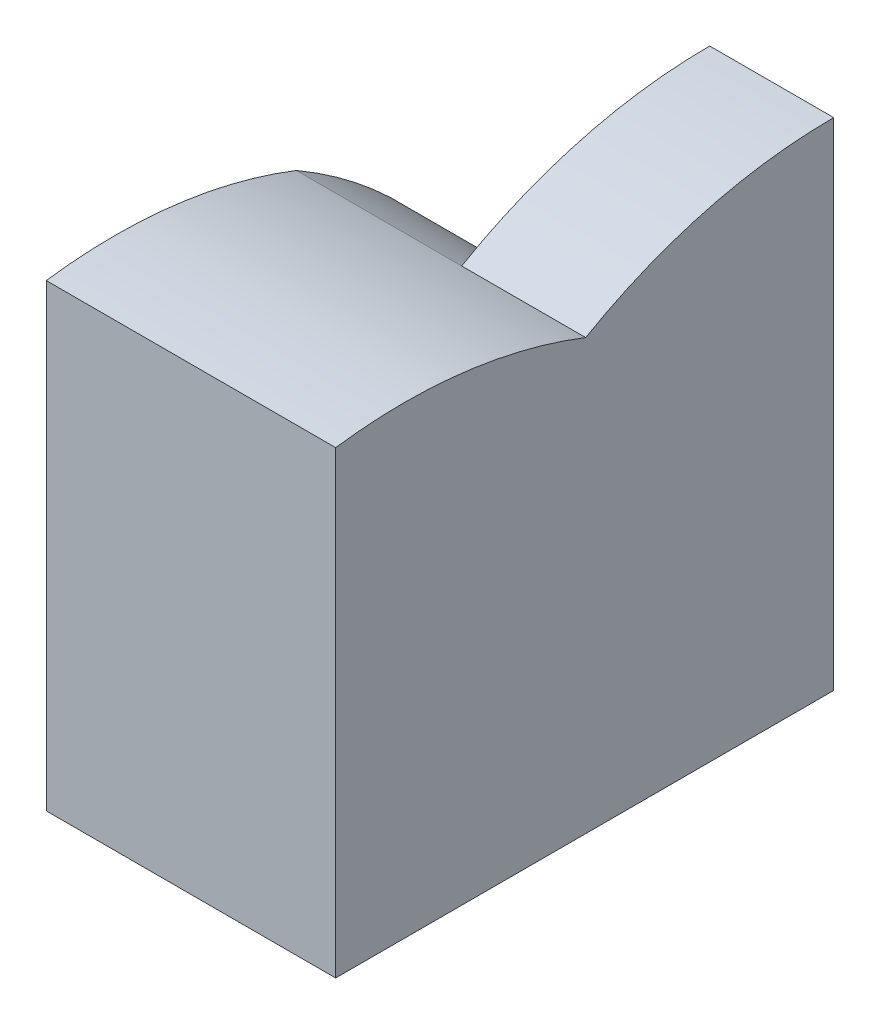
SolidWorks part; units mm, degrees
ref_plane "Front Plane" through (0, 0, 0) normal (0, 0, 1) x (1, 0, 0)
ref_plane "Top Plane" through (0, 0, 0) normal (0, 1, 0) x (1, 0, 0)
ref_plane "Right Plane" through (0, 0, 0) normal (1, 0, 0) x (0, 0, -1)
sketch "Sketch1" plane through (0, 0, 0) normal (1, 0, 0) x (0, 0, -1)
  line L0 (-6, 0) -> (0, 0)
  line L1 (0, 0) -> (0, 6)
  line L2 (-3, 0) -> (-3, 5.1962)
  arc A0 (-6, 0) -> (0, 6) centre (0, 0) cw
  dimension "D2" = 6
  dimension "D3" = 6
  dimension "D1" = 6
extrude "Boss-Extrude1" add sketch "Sketch1" against normal blind 1.5 contours A0 L2 L0 L1
sketch "Sketch2" plane through (0, 0, 0) normal (1, 0, 0) x (0, 0, -1)
  line L0 (-3, 0) -> (-6.0236, 0)
  line L1 (-3, 5.1962) -> (-3, 0)
  arc A0 (-6.0236, 0) -> (-3, 5.1962) centre (-0.0236, -0.0136) cw
  dimension "D1" = 6
extrude "Boss-Extrude2" add sketch "Sketch2" against normal blind 3.5
sketch "Sketch3" plane through (-3.5, 0, 0) normal (-1, 0, 0) x (0, 0, 1)
  line L0 (0, 0) -> (6.0236, 0)
  line L1 (6.0236, 0) -> (6.0236, 6)
  line L2 (3, 5.1962) -> (3, 0)
  arc A0 (0, 0) -> (3, 5.1962) centre (6, 0) cw
  line M5 (3, 5.1962) -> (3, 0)
  dimension "D1" = 6
extrude "Boss-Extrude3" add sketch "Sketch3" against normal blind 3.5 contours A0 L0 M5
sketch "Sketch4" plane through (-3.5, 0, 0) normal (-1, 0, 0) x (0, 0, 1)
  line L0 (6.0236, 0) -> (6.0236, 5.555)
  line L1 (6.0236, 0) -> (3, 0)
  line L3 (3, 0) -> (3, 5.1962)
  arc A1 (3, 5.1962) -> (6.0236, 5.555) centre (5.1957, -0.3876) cw
  dimension "D1" = 6
extrude "Boss-Extrude4" add sketch "Sketch4" against normal blind 3.5
